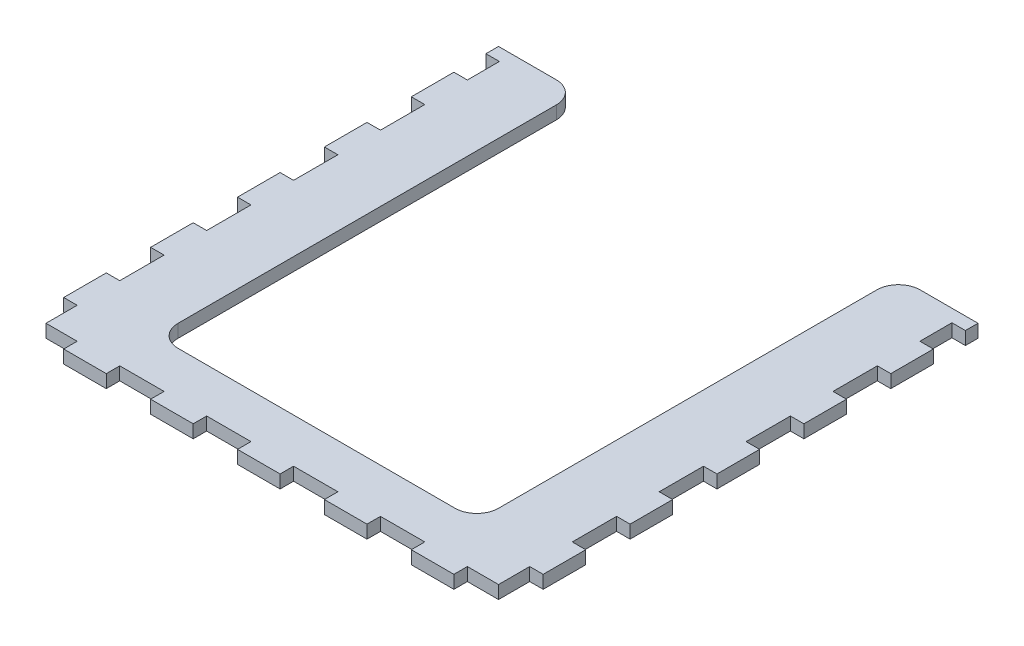
SolidWorks part; units mm, degrees
ref_plane "Front Plane" through (0, 0, 0) normal (0, 0, 1) x (1, 0, 0)
ref_plane "Top Plane" through (0, 0, 0) normal (0, 1, 0) x (1, 0, 0)
ref_plane "Right Plane" through (0, 0, 0) normal (1, 0, 0) x (0, 0, -1)
sketch "Sketch1" plane through (0, 0, 0) normal (0, 1, 0) x (1, 0, 0)
  line L0 (0, 0) -> (0, 21) construction
  line L1 (-55.1722, 43.5014) -> (55.1722, 43.5014) construction
  line L2 (55.1722, 43.5014) -> (55.1722, -66.843) construction
  line L3 (-55.1722, -66.843) -> (55.1722, -66.843) construction
  line L4 (-55.1722, 43.5014) -> (-55.1722, -66.843) construction
  line L5 (-36.8722, 43.5014) -> (-36.8722, -66.843) construction
  line L6 (36.8722, 43.5014) -> (36.8722, -66.843) construction
  line L7 (-55.1722, 43.5014) -> (-41.8722, 43.5014)
  line L8 (55.1722, 43.5014) -> (55.1722, -66.843)
  line L9 (-55.1722, -66.843) -> (-36.8722, -66.843) construction
  line L10 (-55.1722, 43.5014) -> (-55.1722, -66.843)
  line L11 (-36.8722, 43.5014) -> (-36.8722, -66.843) construction
  line L12 (36.8722, 43.5014) -> (36.8722, -66.843) construction
  line L13 (41.8722, 43.5014) -> (55.1722, 43.5014)
  line L14 (36.8722, -66.843) -> (55.1722, -66.843) construction
  line L15 (55.1722, -48.543) -> (-55.1722, -48.543) construction
  line L16 (-55.1722, -48.543) -> (55.1722, -48.543) construction
  line L17 (-55.1722, -66.843) -> (55.1722, -66.843)
  line L18 (36.8722, 38.5014) -> (36.8722, -48.543)
  line L19 (31.8722, -53.543) -> (-31.8722, -53.543)
  line L20 (-36.8722, -48.543) -> (-36.8722, 38.5014)
  circle A0 centre (0, 0) radius 21 construction
  circle A1 centre (0, 0) radius 21 construction
  arc A2 (36.8722, 38.5014) -> (41.8722, 43.5014) centre (41.8722, 38.5014) cw
  arc A3 (-41.8722, 43.5014) -> (-36.8722, 38.5014) centre (-41.8722, 38.5014) cw
  arc A4 (-36.8722, -48.543) -> (-31.8722, -53.543) centre (-31.8722, -48.543) ccw
  arc A5 (31.8722, -53.543) -> (36.8722, -48.543) centre (31.8722, -48.543) ccw
  point P28 (-36.8722, -53.543)
  point P31 (36.8722, -53.543)
  dimension "D1" = 5
  dimension "D2" = 13.3
extrude "Boss-Extrude1" add sketch "Sketch1" against normal up to vertex (3 mm away)
sketch "Sketch3" plane through (0, 0, 0) normal (0, 1, 0) x (1, 0, 0)
  line L0 (52.0722, -46.7708) -> (55.2722, -46.7708)
  line L1 (52.0722, -56.5708) -> (55.2722, -56.5708)
  line L3 (35.1, -63.743) -> (24.9, -63.743)
  line L4 (52.0722, 13.2292) -> (55.2722, 13.2292)
  line L5 (55.2722, 13.2292) -> (55.2722, 23.4292)
  line L6 (55.2722, 23.4292) -> (52.0722, 23.4292)
  line L7 (52.0722, 23.4292) -> (52.0722, 13.2292)
  line L8 (52.0722, 13.2292) -> (55.2722, 13.2292)
  line L9 (55.2722, 13.2292) -> (55.2722, 23.4292)
  line L10 (55.2722, 23.4292) -> (52.0722, 23.4292)
  line L11 (52.0722, 23.4292) -> (52.0722, 13.2292)
  line L12 (55.2722, 3.4292) -> (52.0722, 3.4292)
  line L13 (55.2722, -6.7708) -> (55.2722, 3.4292)
  line L14 (52.0722, -6.7708) -> (55.2722, -6.7708)
  line L15 (52.0722, 3.4292) -> (52.0722, -6.7708)
  line L16 (55.2722, 3.4292) -> (52.0722, 3.4292)
  line L17 (55.2722, -6.7708) -> (55.2722, 3.4292)
  line L18 (52.0722, -6.7708) -> (55.2722, -6.7708)
  line L19 (52.0722, 3.4292) -> (52.0722, -6.7708)
  line L20 (52.0722, 33.2292) -> (55.2722, 33.2292)
  line L21 (55.2722, 33.2292) -> (55.2722, 43.6014)
  line L22 (55.2722, 43.6014) -> (52.0722, 43.6014)
  line L23 (52.0722, 43.6014) -> (52.0722, 33.2292)
  line L24 (52.0722, 33.2292) -> (55.2722, 33.2292)
  line L25 (55.2722, 33.2292) -> (55.2722, 43.6014) construction
  line L26 (55.2722, 43.6014) -> (52.0722, 43.6014) construction
  line L27 (52.0722, 43.6014) -> (52.0722, 33.2292) construction
  line L28 (35.1, -63.743) -> (35.1, -66.943)
  line L29 (35.1, -66.943) -> (24.9, -66.943)
  line L30 (24.9, -63.743) -> (24.9, -66.943)
  line L31 (52.0722, -56.5708) -> (52.0722, -63.743)
  line L32 (15.1, -63.743) -> (4.9, -63.743)
  line L33 (15.1, -63.743) -> (15.1, -66.943)
  line L34 (15.1, -66.943) -> (4.9, -66.943)
  line L35 (4.9, -63.743) -> (4.9, -66.943)
  line L36 (44.9, -63.743) -> (52.0722, -63.743)
  line L37 (44.9, -63.743) -> (44.9, -66.943)
  line L38 (0, -11.6708) -> (0, 43.5014) construction
  line L39 (0, -11.6708) -> (0, 43.5014) construction
  line L40 (55.2722, -46.7708) -> (55.2722, -36.5708)
  line L41 (52.1722, -56.5708) -> (52.1722, -56.6708) construction
  line L42 (52.1722, -56.6708) -> (52.0722, -56.6708) construction
  line L43 (45, -63.743) -> (45, -63.843) construction
  line L44 (45, -63.843) -> (44.9, -63.843) construction
  line L45 (52.1722, -46.6708) -> (52.1722, -46.7708) construction
  line L46 (25, -63.843) -> (24.9, -63.843) construction
  line L47 (35, -63.843) -> (35.1, -63.843) construction
  line L48 (5, -63.843) -> (4.9, -63.843) construction
  line L49 (15, -63.843) -> (15.1, -63.843) construction
  line L50 (45, 40.5014) -> (55.2722, 40.5014) construction
  line L51 (52.0722, 40.6014) -> (55.2722, 40.6014)
  line L52 (55.2722, -26.7708) -> (55.2722, -16.5708)
  line L53 (52.0722, -26.7708) -> (55.2722, -26.7708)
  line L54 (52.0722, -16.5708) -> (52.0722, -26.7708)
  line L55 (55.2722, -16.5708) -> (52.0722, -16.5708)
  line L56 (55.2722, -26.7708) -> (55.2722, -16.5708)
  line L57 (52.0722, -26.7708) -> (55.2722, -26.7708)
  line L58 (52.0722, -16.5708) -> (52.0722, -26.7708)
  line L59 (55.2722, -16.5708) -> (52.0722, -16.5708)
  line L60 (53.6722, 40.5014) -> (53.6722, 40.6014) construction
  line L61 (52.0722, 40.6014) -> (52.0722, 33.2292)
  line L62 (55.2722, 40.6014) -> (55.2722, 33.2292)
  line L63 (-52.0722, 40.6014) -> (-55.2722, 40.6014)
  line L64 (-52.0722, 40.6014) -> (-52.0722, 33.2292)
  line L65 (-52.0722, 33.2292) -> (-55.2722, 33.2292)
  line L66 (-55.2722, 40.6014) -> (-55.2722, 33.2292)
  line L67 (-15.1, -63.743) -> (-15.1, -66.943)
  line L68 (-52.0722, 3.4292) -> (-55.2722, 3.4292)
  line L69 (-55.2722, 3.4292) -> (-55.2722, -6.7708)
  line L70 (-55.2722, -6.7708) -> (-52.0722, -6.7708)
  line L71 (-52.0722, -6.7708) -> (-52.0722, 3.4292)
  line L72 (-52.0722, 3.4292) -> (-55.2722, 3.4292)
  line L73 (-55.2722, 3.4292) -> (-55.2722, -6.7708)
  line L74 (-55.2722, -6.7708) -> (-52.0722, -6.7708)
  line L75 (-52.0722, -6.7708) -> (-52.0722, 3.4292)
  line L76 (-55.2722, 13.2292) -> (-52.0722, 13.2292)
  line L77 (-55.2722, 23.4292) -> (-55.2722, 13.2292)
  line L78 (-52.0722, 23.4292) -> (-55.2722, 23.4292)
  line L79 (-52.0722, 13.2292) -> (-52.0722, 23.4292)
  line L80 (-55.2722, 13.2292) -> (-52.0722, 13.2292)
  line L81 (-55.2722, 23.4292) -> (-55.2722, 13.2292)
  line L82 (-52.0722, 23.4292) -> (-55.2722, 23.4292)
  line L83 (-52.0722, 13.2292) -> (-52.0722, 23.4292)
  line L84 (-15.1, -63.743) -> (-4.9, -63.743)
  line L85 (-4.9, -63.743) -> (-4.9, -66.943)
  line L86 (-15.1, -66.943) -> (-4.9, -66.943)
  line L87 (-35.1, -63.743) -> (-35.1, -66.943)
  line L88 (-35.1, -63.743) -> (-24.9, -63.743)
  line L89 (-24.9, -63.743) -> (-24.9, -66.943)
  line L90 (-35.1, -66.943) -> (-24.9, -66.943)
  line L91 (-44.9, -66.943) -> (-55.2722, -66.943)
  line L92 (-44.9, -63.743) -> (-44.9, -66.943)
  line L93 (-44.9, -63.743) -> (-52.0722, -63.743)
  line L94 (-52.0722, -56.5708) -> (-52.0722, -63.743)
  line L95 (-52.0722, -56.5708) -> (-55.2722, -56.5708)
  line L96 (-55.2722, -66.943) -> (-55.2722, -56.5708)
  line L97 (-52.0722, -46.7708) -> (-55.2722, -46.7708)
  line L98 (-52.0722, -36.5708) -> (-52.0722, -46.7708)
  line L99 (-55.2722, -36.5708) -> (-52.0722, -36.5708)
  line L100 (-55.2722, -46.7708) -> (-55.2722, -36.5708)
  line L108 (52.0722, -66.943) -> (55.2722, -66.943)
  line L109 (55.2722, -66.943) -> (55.2722, -36.5708)
  line L110 (55.2722, -36.5708) -> (52.0722, -36.5708)
  line L111 (52.0722, -36.5708) -> (52.0722, -66.943)
  line L112 (44.9, -66.943) -> (55.2722, -66.943)
  line L113 (55.2722, -66.943) -> (55.2722, -56.5708)
  line L114 (55.2722, -36.5708) -> (52.0722, -36.5708)
  line L115 (52.0722, -36.5708) -> (52.0722, -46.7708)
  line L124 (-55.2722, -26.7708) -> (-52.0722, -26.7708)
  line L125 (-55.2722, -16.5708) -> (-55.2722, -26.7708)
  line L126 (-52.0722, -16.5708) -> (-55.2722, -16.5708)
  line L127 (-52.0722, -26.7708) -> (-52.0722, -16.5708)
  line L128 (-55.2722, -26.7708) -> (-52.0722, -26.7708)
  line L129 (-55.2722, -16.5708) -> (-55.2722, -26.7708)
  line L130 (-52.0722, -16.5708) -> (-55.2722, -16.5708)
  line L131 (-52.0722, -26.7708) -> (-52.0722, -16.5708)
  dimension "D1" = 0
  dimension "D2" = 0
  dimension "D3" = 0
  dimension "D7" = 0
  dimension "D9" = 0
  dimension "D10" = 0
  dimension "D14" = 0
  dimension "D16" = 0
extrude "Cut-Extrude1" cut sketch "Sketch3" against normal through all
